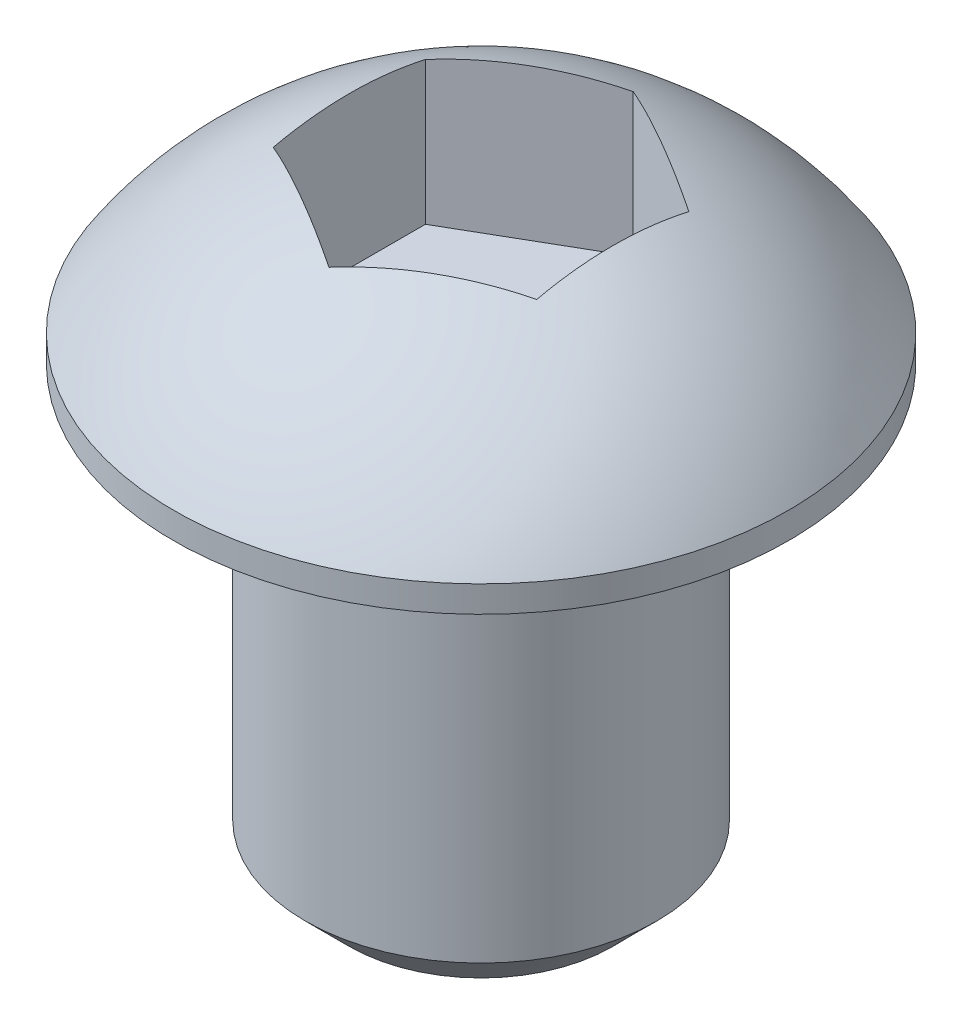
SolidWorks part; units mm, degrees
material "1.6523 (20NiCrMoS2-2)"
ref_plane "Front Plane" through (0, 0, 0) normal (0, 0, 1) x (1, 0, 0)
ref_plane "Top Plane" through (0, 0, 0) normal (0, 1, 0) x (1, 0, 0)
ref_plane "Right Plane" through (0, 0, 0) normal (1, 0, 0) x (0, 0, -1)
sketch "Sketch1" plane through (0, 0, 0) normal (0, 1, 0) x (1, 0, 0)
  circle A0 centre (0, 0) radius 2
  circle A1 centre (0, 0) radius 3.5
  dimension "D1" = 4
  dimension "D2" = 7
extrude "Boss-Extrude3" add sketch "Sketch1" against normal blind 5 contours A0
sketch "Sketch3" plane through (0, 0, 0) normal (0, 0, 1) x (1, 0, 0)
  line L0 (-3.5, 0) -> (-3.5, 0.3)
  line L1 (3.5, 0) -> (-3.5, 0) construction
  line L4 (0, -2) -> (0, 2.3599) construction
  line L5 (-3.5, 0) -> (0, 0)
  line L6 (0, 2.1881) -> (0, 0)
  arc A0 (-3.5, 0.3) -> (0, 2.1881) centre (0, -2) cw
  dimension "D1" = 7
  dimension "D2" = 0.3
  dimension "D3" = 2
revolve "Revolve2" add sketch "Sketch3" angle 360 about L4
chamfer "Chamfer2" distance 0.5 angle 45 1 edges at (0, -5, 2)
ref_plane "Plane1" through (0, 2.1881, 0) normal (0, 1, 0) x (1, 0, 0)
sketch "Sketch4" plane through (0, 2.1881, 0) normal (0, 1, 0) x (1, 0, 0)
  line L1 (0, 1.7321) -> (-1.5, 0.866)
  line L2 (-1.5, 0.866) -> (-1.5, -0.866)
  line L3 (-1.5, -0.866) -> (0, -1.7321)
  line L4 (0, -1.7321) -> (1.5, -0.866)
  line L5 (1.5, -0.866) -> (1.5, 0.866)
  line L6 (1.5, 0.866) -> (0, 1.7321)
  circle A0 centre (0, 0) radius 1.5 construction
  dimension "D1" = 3
extrude "Cut-Extrude2" cut sketch "Sketch4" against normal blind 2
